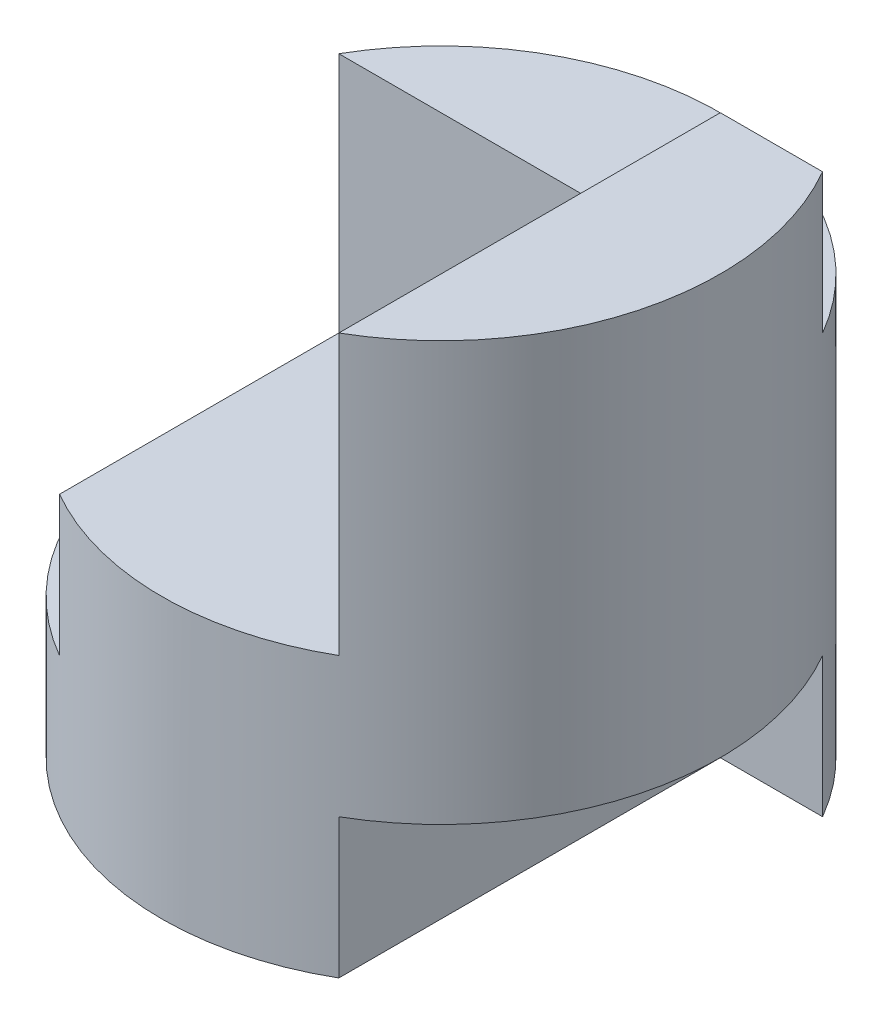
SolidWorks part; units mm, degrees
ref_plane "Front" through (0, 0, 0) normal (0, 0, 1) x (1, 0, 0)
ref_plane "Top" through (0, 0, 0) normal (0, 1, 0) x (1, 0, 0)
ref_plane "Right" through (0, 0, 0) normal (1, 0, 0) x (0, 0, -1)
sketch "Sketch1" plane through (0, 0, 0) normal (0, 1, 0) x (1, 0, 0)
  circle A0 centre (0, 0) radius 2
  dimension "D1" = 4
extrude "Boss-Extrude1" add sketch "Sketch1" along normal blind 4
sketch "Sketch2" plane through (0, 0, 0) normal (0, 0, 1) x (1, 0, 0)
  line L0 (-2, 4) -> (1, 4)
  line L2 (2, 0) -> (2, 4) construction
  line L3 (2, 1) -> (1, 1)
  line L5 (1, 2) -> (-1, 2)
  line L8 (-2, 3) -> (-2, 4)
  line L9 (-2, 1) -> (-1, 1)
  line L14 (1, 1) -> (2, 1)
  line L15 (1, 1) -> (1, 0)
  line L16 (1, 0) -> (2, 0)
  line L17 (2, 1) -> (2, 0)
  line L18 (-2, 4) -> (-2, 0) construction
  line L19 (-1, 1) -> (-1, 2)
  line L20 (-2, 3) -> (-2, 1)
  line L21 (1, 2) -> (1, 3)
  line L22 (1, 3) -> (1, 4)
  dimension "D1" = 1
  dimension "D3" = 1
extrude "Cut-Extrude1" cut sketch "Sketch2" against normal blind 1 and the other way blind 3 contours L21 L22 L0 L8 L20 L9 L19 L5 | L17 L3 L15 L16
sketch "Sketch5" plane through (0, 4, 0) normal (0, 1, 0) x (1, 0, 0)
  line L0 (-1.7321, 1) -> (1.7321, 1)
  arc A0 (-1.7321, 1) -> (1.7321, 1) centre (0, 0) cw
extrude "Cut-Extrude4" cut sketch "Sketch5" against normal blind 1
